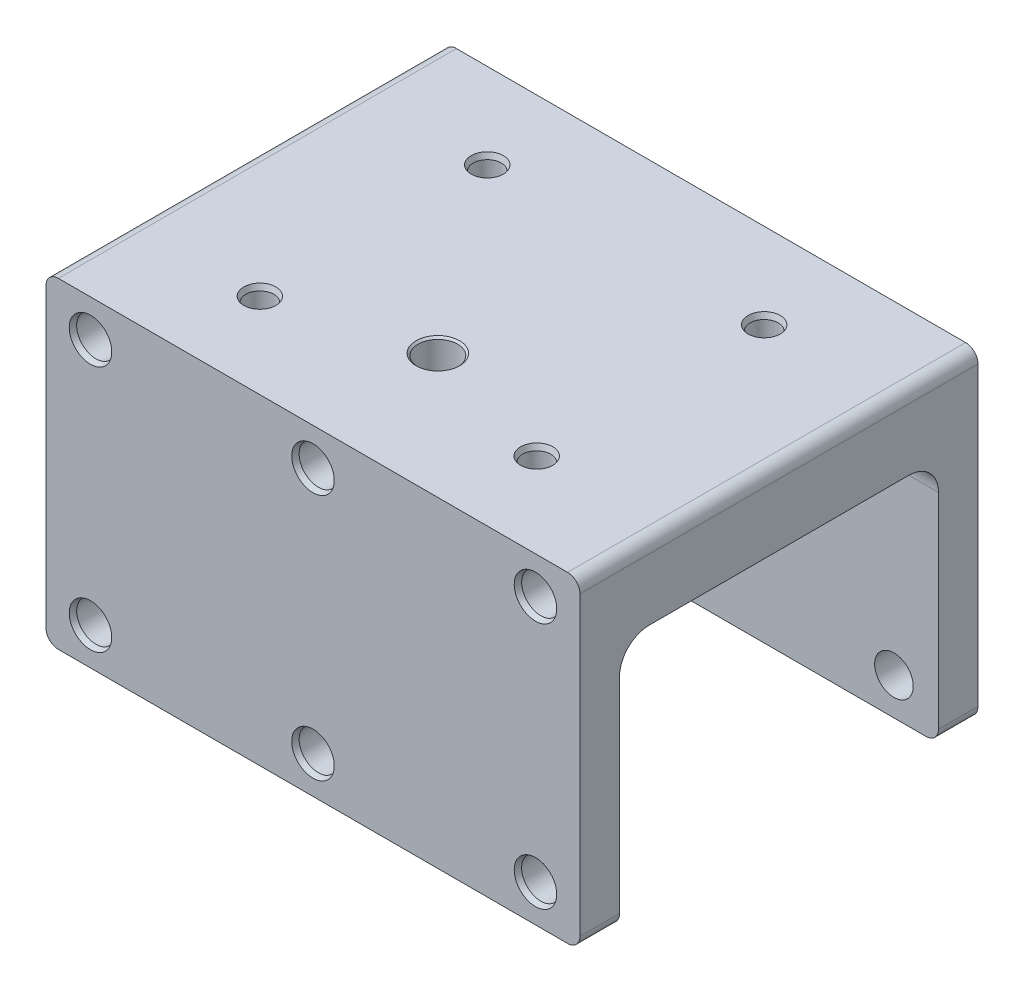
SolidWorks part; units mm, degrees
ref_plane "Front" through (0, 0, 0) normal (0, 0, 1) x (1, 0, 0)
ref_plane "Top" through (0, 0, 0) normal (0, 1, 0) x (1, 0, 0)
ref_plane "Right" through (0, 0, 0) normal (1, 0, 0) x (0, 0, -1)
sketch "Sketch1" plane through (0, 0, 0) normal (0, 1, 0) x (1, 0, 0)
  line L1 (0, 0) -> (108, 0)
  line L2 (0, 0) -> (0, 80.5)
  line L3 (0, 80.5) -> (108, 80.5)
  line L4 (108, 0) -> (108, 80.5)
  dimension "D1" = 80.5
  dimension "D2" = 108
extrude "Boss-Extrude1" add sketch "Sketch1" along normal blind 15
sketch "Sketch2" plane through (0, 0, 0) normal (0, 0, 1) x (1, 0, 0)
  line L0 (54, 15) -> (54, 0) construction
  line L1 (0, 15) -> (108, 15) construction
  line L2 (0, 0) -> (108, 0) construction
  line L3 (9, 7.5) -> (99, 7.5) construction
  circle A0 centre (9, 7.5) radius 3.9
  circle A1 centre (99, 7.5) radius 3.9
  circle A2 centre (54, 7.5) radius 3.9
  point P9 (54, 7.5)
  dimension "D2" = 7.8
  dimension "D3" = 7.8
  dimension "D1" = 90
extrude "Cut-Extrude1" cut sketch "Sketch2" against normal blind 7
sketch "Sketch3" plane through (0, 0, 0) normal (0, 0, 1) x (1, 0, 0)
  line L0 (108, 15) -> (108, 0) construction
  line L1 (0, 0) -> (108, 0)
  line L2 (0, 0) -> (0, -50)
  line L3 (0, -50) -> (108, -50)
  line L4 (108, 0) -> (108, -50)
  line L5 (0, -42.5) -> (108, -42.5) construction
  line L6 (0, 15) -> (108, 15) construction
  line L7 (0, 15) -> (108, 15) construction
  line L8 (9, 7.5) -> (9, -42.5) construction
  line L9 (99, 7.5) -> (99, -42.5) construction
  circle A0 centre (99, 7.5) radius 3.9 construction
  circle A1 centre (99, 7.5) radius 3.9 construction
  circle A2 centre (99, 7.5) radius 3.9 construction
  circle A3 centre (99, -42.5) radius 3.9
  circle A4 centre (54, -42.5) radius 3.9
  circle A5 centre (9, -42.5) radius 3.9
  dimension "D1" = 50
  dimension "D2" = 7.5
  dimension "D3" = 7.5
extrude "Boss-Extrude2" add sketch "Sketch3" against normal blind 8
ref_plane "Plane1" through (0, 0, -40.25) normal (0, 0, 1) x (1, 0, 0)
mirror "Mirror1" about plane through (0, 0, -40.25) normal (0, 0, 1) of "Boss-Extrude2", "Cut-Extrude1"
chamfer "Chamfer1" distance 0.4 angle 70 12 edges at (102.9, 7.5, -80.5) (12.9, 7.5, -80.5) (102.9, 7.5, 0) (12.9, 7.5, 0) (57.9, 7.5, -80.5) (57.9, 7.5, 0) (12.9, -42.5, -80.5) (57.9, -42.5, -80.5) (102.9, -42.5, -80.5) (57.9, -42.5, 0) (12.9, -42.5, 0) (102.9, -42.5, 0)
fillet "Fillet1" radius 2.5 6 edges at (0, 15, -40.25) (108, 15, -40.25) (0, -50, -76.5) (0, -50, -4) (108, -50, -76.5) (108, -50, -4)
fillet "Fillet2" radius 6 2 edges at (54, 0, -72.5) (54, 0, -8)
sketch "Sketch4" plane through (0, 15, 0) normal (0, 1, 0) x (1, 0, 0)
  line L0 (54, 0) -> (54, 80.5) construction
  line L1 (2.5, 0) -> (105.5, 0) construction
  line L2 (105.5, 80.5) -> (2.5, 80.5) construction
  line L4 (26, 63.25) -> (82, 63.25) construction
  line L5 (26, 63.25) -> (26, 17.25) construction
  line L6 (26, 17.25) -> (82, 17.25) construction
  line L7 (82, 63.25) -> (82, 17.25) construction
  line L8 (26, 63.25) -> (82, 17.25) construction
  line L9 (26, 17.25) -> (82, 63.25) construction
  circle A0 centre (82, 17.25) radius 2.85
  circle A1 centre (26, 17.25) radius 2.85
  circle A2 centre (26, 63.25) radius 2.85
  circle A3 centre (82, 63.25) radius 2.85
  point P6 (54, 40.25)
  dimension "D4" = 5.7
  dimension "D1" = 46
  dimension "D2" = 56
  dimension "D3" = 17.25
extrude "Cut-Extrude2" cut sketch "Sketch4" against normal blind 11
chamfer "Chamfer2" distance 0.4 angle 70 4 edges at (26, 15, -60.4) (82, 15, -60.4) (26, 15, -14.4) (82, 15, -14.4)
sketch "Sketch5" plane through (0, 15, 0) normal (0, 1, 0) x (1, 0, 0)
  line L0 (82, 17.25) -> (26, 17.25) construction
  line L1 (54, 17.25) -> (54, 25.25) construction
  circle A0 centre (54, 25.25) radius 4
  dimension "D2" = 8
  dimension "D1" = 8
extrude "Cut-Extrude3" cut sketch "Sketch5" against normal through all
chamfer "Chamfer3" distance 0.4 angle 45 1 edges at (54, 15, -21.25)
equation "\"Length\"= 108"
equation "\"D2@Sketch1\"=\"Length\""
equation "\"Hole_Spacing\"= 90"
equation "\"D1@Sketch2\"=\"Hole_Spacing\""
equation "\"D3@Sketch3\"=\"D2@Sketch3\""
